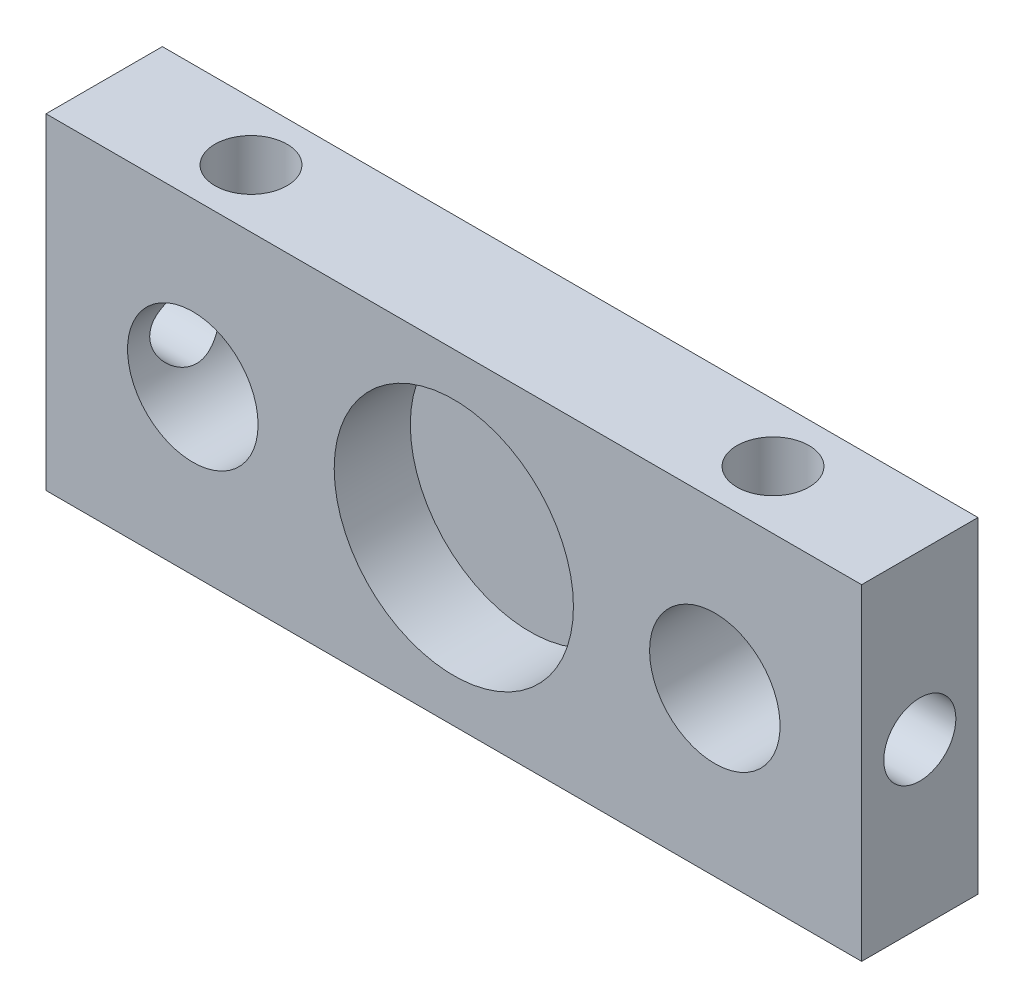
SolidWorks part; units mm, degrees
ref_plane "Plano frontal" through (0, 0, 0) normal (0, 0, 1) x (1, 0, 0)
ref_plane "Plano superior" through (0, 0, 0) normal (0, 1, 0) x (1, 0, 0)
ref_plane "Plano direito" through (0, 0, 0) normal (1, 0, 0) x (0, 0, -1)
sketch "Esboço1" plane through (0, 0, 0) normal (0, 0, 1) x (1, 0, 0)
  line L1 (37.5, -15) -> (-37.5, -15)
  line L2 (37.5, -15) -> (37.5, 15)
  line L3 (37.5, 15) -> (-37.5, 15)
  line L4 (-37.5, -15) -> (-37.5, 15)
  line L5 (37.5, -15) -> (-37.5, 15) construction
  line L6 (37.5, 15) -> (-37.5, -15) construction
  point P0 (0, 0)
  dimension "D1" = 30
  dimension "D2" = 75
extrude "Ressalto-extrusão1" add sketch "Esboço1" along normal blind 10.7
sketch "Esboço2" plane through (0, 0, 10.7) normal (0, 0, 1) x (1, 0, 0)
  line L0 (-35.9706, 0) -> (33.3822, 0) construction
  line L1 (0, -18.6994) -> (0, 18.6101) construction
  circle A0 centre (-24, 0) radius 6
  circle A2 centre (24, 0) radius 6
  dimension "D1" = 12
  dimension "D2" = 24
extrude "Corte-extrusão1" cut sketch "Esboço2" against normal blind 10
sketch "Esboço7" plane through (0, 0, 10.7) normal (0, 0, 1) x (1, 0, 0)
  circle A0 centre (0, 0) radius 11
  dimension "D1" = 22
extrude "Corte-extrusão6" cut sketch "Esboço7" against normal blind 7
hole_wizard "Furo roscado para conduíte de 1/4-281" positions "Esboço8" profile "Esboço9" tap size "1/4-28" standard "Helicoil® Inch"
sketch "Esboço8" plane through (0, 15, 0) normal (0, 1, 0) x (1, 0, 0)
  line L0 (0, 7.4636) -> (0, -13.611) construction
  line L4 (-37.5, -10.7) -> (-37.5, 0) construction
  line L5 (37.5, -10.7) -> (-37.5, -10.7) construction
  point P0 (-24, -5.35)
  point P14 (0, 0)
  point P18 (0, 0)
  point P19 (24, -5.35)
  dimension "D1" = 13.5
  dimension "D2" = 5.35
sketch "Esboço9" plane through (-24, 15, 5.35) normal (1, 0, 0) x (0, 0, 1)
  line L0 (0, 0) -> (0, 16.9917)
  line L1 (0, 16.9917) -> (3.3147, 15)
  line L2 (3.3147, 15) -> (3.3147, 0)
  line L5 (3.3147, 0) -> (0, 0)
  line L10 (0, 16.9917) -> (-3.3147, 15) construction
  line L11 (0, -6.35) -> (0, 107.95) construction
  dimension "Tap Drill Dia." = 6.6294
  dimension "Tap Drill Depth" = 15
  dimension "Drill Angle" = 118
cosmetic thread "Rosca de furo1"
cosmetic thread "Rosca de furo2"
hole_wizard "Furo roscado para conduíte de 1/4-282" positions "Esboço11" profile "Esboço12" tap size "1/4-28" standard "Helicoil® Inch"
sketch "Esboço11" plane through (-37.5, 0, 0) normal (-1, 0, 0) x (0, 0, 1)
  line L0 (10.7, -15) -> (0, -15) construction
  line L1 (10.7, 15) -> (10.7, -15) construction
  point P0 (5.35, 0)
  dimension "D1" = 15
  dimension "D2" = 5.35
sketch "Esboço12" plane through (-37.5, 0, 5.35) normal (0, 1, 0) x (0, 0, 1)
  line L0 (0, 0) -> (0, 16.9517)
  line L1 (0, 16.9517) -> (3.3147, 14.96)
  line L2 (3.3147, 14.96) -> (3.3147, 0)
  line L5 (3.3147, 0) -> (0, 0)
  line L10 (0, 16.9517) -> (-3.3147, 14.96) construction
  line L11 (0, -6.35) -> (0, 107.95) construction
  dimension "Tap Drill Dia." = 6.6294
  dimension "Tap Drill Depth" = 14.96
  dimension "Drill Angle" = 118
cosmetic thread "Rosca de furo3"
hole_wizard "Furo roscado para conduíte de 1/4-283" positions "Esboço13" profile "Esboço14" tap size "1/4-28" standard "Helicoil® Inch"
sketch "Esboço13" plane through (37.5, 0, 0) normal (1, 0, 0) x (0, 0, -1)
  line L0 (0, -15) -> (0, 15) construction
  line L1 (-10.7, 15) -> (0, 15) construction
  point P0 (-5.35, 0)
  dimension "D1" = 5.35
  dimension "D2" = 15
sketch "Esboço14" plane through (37.5, 0, 5.35) normal (0, 1, 0) x (0, 0, -1)
  line L0 (0, 0) -> (0, 16.9917)
  line L1 (0, 16.9917) -> (3.3147, 15)
  line L2 (3.3147, 15) -> (3.3147, 0)
  line L5 (3.3147, 0) -> (0, 0)
  line L10 (0, 16.9917) -> (-3.3147, 15) construction
  line L11 (0, -6.35) -> (0, 107.95) construction
  dimension "Tap Drill Dia." = 6.6294
  dimension "Tap Drill Depth" = 15
  dimension "Drill Angle" = 118
cosmetic thread "Rosca de furo4"
hole_wizard "Furo roscado para conduíte de 1/4-284" positions "Esboço15" profile "Esboço16" tap size "1/4-28" standard "Helicoil® Inch"
sketch "Esboço15" plane through (0, -15, 0) normal (0, -1, 0) x (-1, 0, 0)
  line L0 (37.5, 0) -> (-37.5, 0) construction
  line L1 (37.5, -10.7) -> (37.5, 0) construction
  line L2 (0, 8.0773) -> (0, -16.6613) construction
  point P0 (15, -5.35)
  point P11 (0, 0)
  point P12 (-15, -5.35)
  dimension "D1" = 5.35
  dimension "D2" = 22.5
sketch "Esboço16" plane through (-15, -15, 5.35) normal (1, 0, 0) x (0, 0, -1)
  line L0 (0, 0) -> (0, 13.9917)
  line L1 (0, 13.9917) -> (3.3147, 12)
  line L2 (3.3147, 12) -> (3.3147, 0)
  line L5 (3.3147, 0) -> (0, 0)
  line L10 (0, 13.9917) -> (-3.3147, 12) construction
  line L11 (0, -6.35) -> (0, 107.95) construction
  dimension "Tap Drill Dia." = 6.6294
  dimension "Tap Drill Depth" = 12
  dimension "Drill Angle" = 118
cosmetic thread "Rosca de furo5"
cosmetic thread "Rosca de furo6"
